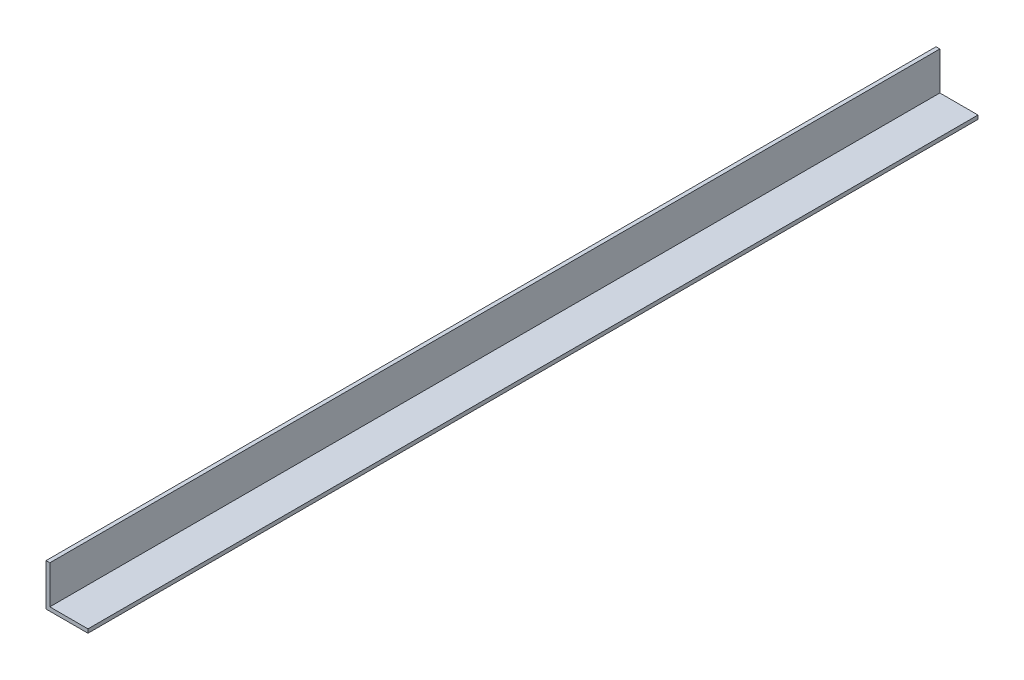
SolidWorks part; units mm, degrees
ref_plane "Спереди" through (0, 0, 0) normal (0, 0, 1) x (1, 0, 0)
ref_plane "Сверху" through (0, 0, 0) normal (0, 1, 0) x (1, 0, 0)
ref_plane "Справа" through (0, 0, 0) normal (1, 0, 0) x (0, 0, -1)
sketch "Эскиз1" plane through (0, 0, 0) normal (0, 0, 1) x (1, 0, 0)
  line L0 (0, 30) -> (0, 0)
  line L1 (0, 0) -> (30, 0)
extrude "Вытянуть-Тонкостенный1" add sketch "Эскиз1" along normal blind 700 thin
